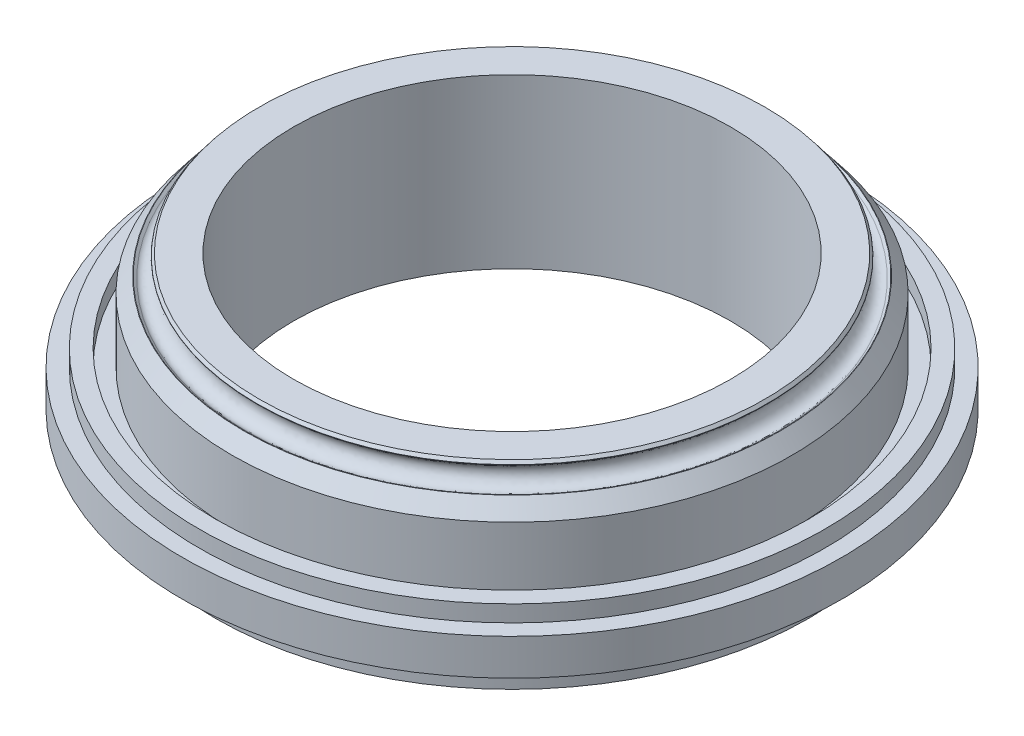
SolidWorks part; units mm, degrees
ref_plane "Front Plane" through (0, 0, 0) normal (0, 0, 1) x (1, 0, 0)
ref_plane "Top Plane" through (0, 0, 0) normal (0, 1, 0) x (1, 0, 0)
ref_plane "Right Plane" through (0, 0, 0) normal (1, 0, 0) x (0, 0, -1)
sketch "Sketch1" plane through (0, 0, 0) normal (0, 0, 1) x (1, 0, 0)
  line L0 (0, 0) -> (0, 38.71) construction
  line L2 (66.3265, 40.7481) -> (76.75, 40.7481)
  line L3 (76.75, 40.7481) -> (77.4739, 39.8142)
  line L5 (84.99, 10.7376) -> (89.9, 10.7376)
  line L6 (89.9, 10.7376) -> (89.9, 15.7376)
  line L7 (89.9, 15.7376) -> (95, 15.7376)
  line L8 (95, 15.7376) -> (95, 10.7376)
  line L9 (95, 10.7376) -> (100, 10.7376)
  line L10 (100, 10.7376) -> (100, -0.2624)
  line L27 (66.3265, -0.2624) -> (100, -0.2624) construction
  line L31 (66.3265, 40.7481) -> (66.3265, -10.2624)
  line L32 (78.5765, 38.3918) -> (78.5765, 27.8011) construction
  line L33 (80.5216, 34.1423) -> (81.3641, 34.7954)
  line L34 (76.6313, 39.1611) -> (77.4739, 39.8142)
  line L35 (81.3641, 34.7954) -> (84.99, 30.1175)
  line L36 (77.635, 39.6063) -> (81.203, 35.0032)
  line L37 (66.3265, -10.2624) -> (90, -10.2624)
  line L38 (90, -10.2624) -> (90, -0.2624)
  line L39 (90, -0.2624) -> (100, -0.2624)
  line L40 (84.99, 10.7376) -> (84.99, 30.1175)
  circle A0 centre (78.5765, 36.6517) radius 2.665 construction
  circle A1 centre (78.55, -10.2624) radius 2.665 construction
  ellipse E0 centre (78.5765, 36.6517) end of major axis (76.6313, 39.1611) minor radius 2.675
  ellipse E1 centre (78.55, -10.2624) end of major axis (81.8, -10.2624) minor radius 2.165
  point P7 (0, 0)
  point P29 (0, 0)
  point P36 (0, 0)
  dimension "D17" = 5.33
  dimension "D18" = 41.0105
  dimension "D16" = 3.25
  dimension "D3" = 5.33
  dimension "D22" = 90
  dimension "D1" = 100
  dimension "D4" = 84.99
  dimension "D5" = 89.9
  dimension "D6" = 5.1
  dimension "D7" = 38.71
  dimension "D8" = 11
  dimension "D9" = 40.7481
  dimension "D10" = 5
  dimension "D11" = 19.3799
  dimension "D13" = 66.3265
  dimension "D14" = 1.066
  dimension "D15" = 76.75
  dimension "D19" = 3.175
  dimension "D20" = 2.675
  dimension "D21" = 78.55
  dimension "D23" = 10
  dimension "D24" = 2.165
revolve "Revolve1" add sketch "Sketch1" angle 360 about L0
fillet "Fillet2" radius 0.1 2 edges at (0, 34.7954, -81.3641) (0, 39.8142, -77.4739)
sketch "Sketch2" plane through (0, -10.2624, 0) normal (0, -1, 0) x (1, 0, 0)
  circle A0 centre (0, 85) radius 1.55
  circle A1 centre (0, 0) radius 85 construction
  circle A2 centre (42.5, 73.6122) radius 1.55
  circle A3 centre (73.6122, 42.5) radius 1.55
  circle A4 centre (85, 0) radius 1.55
  circle A5 centre (73.6122, -42.5) radius 1.55
  circle A6 centre (42.5, -73.6122) radius 1.55
  circle A7 centre (0, -85) radius 1.55
  circle A8 centre (-42.5, -73.6122) radius 1.55
  circle A9 centre (-73.6122, -42.5) radius 1.55
  circle A10 centre (-85, 0) radius 1.55
  circle A11 centre (-73.6122, 42.5) radius 1.55
  circle A12 centre (-42.5, 73.6122) radius 1.55
  point P30 (0, 0)
  dimension "D1" = 170
  dimension "D2" = 3.1
  dimension "D3" = 12
extrude "Cut-Extrude1" cut sketch "Sketch2" against normal blind 10
